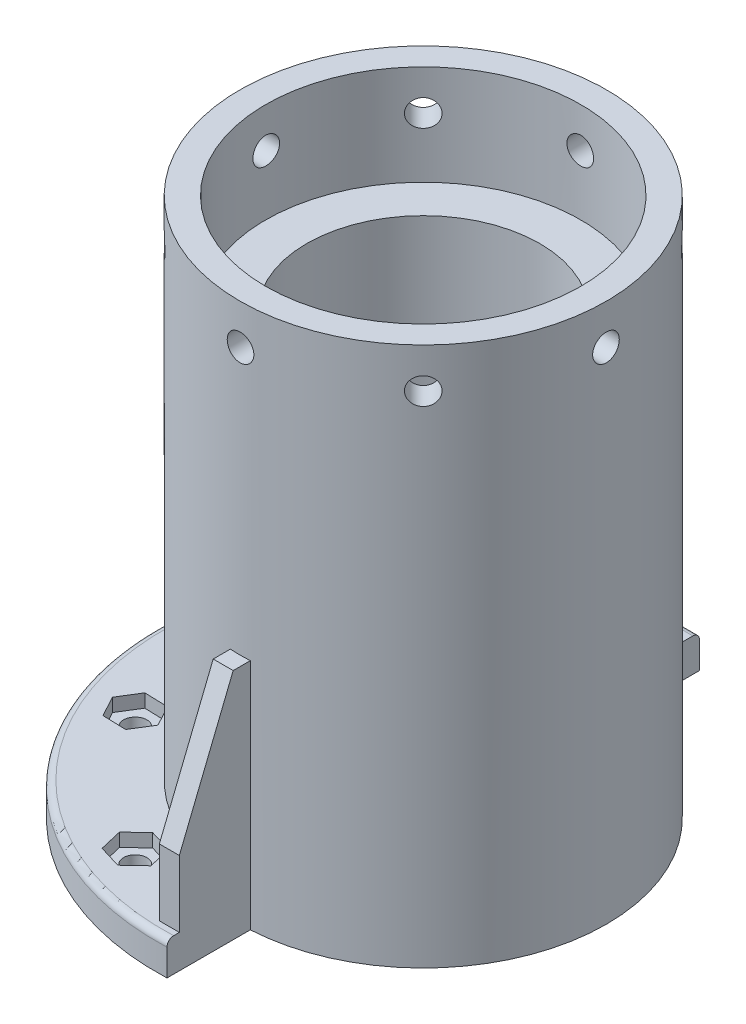
SolidWorks part; units mm, degrees
ref_plane "Front Plane" through (0, 0, 0) normal (0, 0, 1) x (1, 0, 0)
ref_plane "Top Plane" through (0, 0, 0) normal (0, 1, 0) x (1, 0, 0)
ref_plane "Right Plane" through (0, 0, 0) normal (1, 0, 0) x (0, 0, -1)
sketch "Sketch1" plane through (0, 0, 0) normal (0, 1, 0) x (1, 0, 0)
  circle A0 centre (0, 0) radius 23.65
  circle A1 centre (0, 0) radius 27.5
  dimension "D1" = 47.3
  dimension "D2" = 55
extrude "Boss-Extrude1" add sketch "Sketch1" along normal blind 30
sketch "Sketch2" plane through (0, 0, 0) normal (0, 0, 1) x (1, 0, 0)
  line L0 (27.5, 30) -> (-27.5, 30) construction
  circle A0 centre (0, 24) radius 2
  dimension "D2" = 4
  dimension "D1" = 6
extrude "Cut-Extrude1" cut sketch "Sketch2" against normal through all both and the other way through all
pattern_circular "CirPattern1" count 4 every 45 about axis through (0, 30, 0) along (0, 1, 0) of "Cut-Extrude1"
sketch "Sketch3" plane through (0, 0, 0) normal (0, -1, 0) x (1, 0, 0)
  circle A0 centre (0, 0) radius 27.5
  circle A1 centre (0, 0) radius 23.65
extrude "Boss-Extrude2" add sketch "Sketch3" along normal blind 51
sketch "Sketch4" plane through (0, -51, 0) normal (0, -1, 0) x (1, 0, 0)
  line L0 (1.5, 39.9719) -> (1.5, -39.9719)
  arc A0 (1.5, 39.9719) -> (1.5, -39.9719) centre (0, 0) ccw
  circle M1 centre (0, 0) radius 27.5
  dimension "D1" = 80
  dimension "D2" = 1.5
extrude "Boss-Extrude3" add sketch "Sketch4" against normal blind 5 contours L0 A0 M1 | L0 M1
sketch "Sketch6" plane through (0, -46, 0) normal (0, 1, 0) x (1, 0, 0)
  line L0 (1.5, 27.4591) -> (1.5, 39.9719) construction
  line L1 (1.5, 36.6445) -> (-1.5, 36.6445)
  line L2 (1.5, 36.6445) -> (1.5, 24.6445)
  line L3 (1.5, 24.6445) -> (-1.5, 24.6445)
  line L4 (-1.5, 36.6445) -> (-1.5, 24.6445)
  line L5 (1.5, -39.9719) -> (1.5, -27.4591) construction
  line L6 (-36.7098, 1.2195) -> (-24.7098, 1.2195)
  line L7 (-36.7098, 1.2195) -> (-36.7098, -1.7805)
  line L8 (-36.7098, -1.7805) -> (-24.7098, -1.7805)
  line L9 (-24.7098, 1.2195) -> (-24.7098, -1.7805)
  line L10 (1.5, -38.1145) -> (-1.5, -38.1145)
  line L11 (1.5, -38.1145) -> (1.5, -26.1145)
  line L12 (1.5, -26.1145) -> (-1.5, -26.1145)
  line L13 (-1.5, -38.1145) -> (-1.5, -26.1145)
  dimension "D1" = 3
  dimension "D2" = 12
  dimension "D3" = 12
  dimension "D4" = 3
  dimension "D5" = 3
  dimension "D6" = 12
extrude "Boss-Extrude4" add sketch "Sketch6" along normal blind 30
chamfer "Chamfer1" distance 20 angle 22 3 edges at (0, -16, -36.6445) (-36.7098, -16, 0.2805) (0, -16, 38.1145)
sketch "Sketch7" plane through (0, -46, 0) normal (0, 1, 0) x (1, 0, 0)
  line L0 (0, 0) -> (-12.6635, 30.5724) construction
  line L1 (1.5, 36.6445) -> (1.5, 39.9719) construction
  circle A0 centre (-12.6635, 30.5724) radius 1.75
  dimension "D1" = 3.5
  dimension "D2" = 22.5
extrude "Cut-Extrude2" cut sketch "Sketch7" against normal through all
sketch "Sketch8" plane through (0, -46, 0) normal (0, 1, 0) x (1, 0, 0)
  line L1 (-9.5616, 32.2402) -> (-12.5569, 34.0926)
  line L2 (-12.5569, 34.0926) -> (-15.6588, 32.4249)
  line L3 (-15.6588, 32.4249) -> (-15.7654, 28.9046)
  line L4 (-15.7654, 28.9046) -> (-12.7701, 27.0522)
  line L5 (-12.7701, 27.0522) -> (-9.6682, 28.72)
  line L6 (-9.6682, 28.72) -> (-9.5616, 32.2402)
  circle A0 centre (-12.6635, 30.5724) radius 3.05 construction
  dimension "D1" = 6.1
extrude "Cut-Extrude3" cut sketch "Sketch8" against normal blind 2
pattern_circular "CirPattern2" count 4 every 45 about axis through (0, 0, 0) along (0, 1, 0) of "Cut-Extrude2", "Cut-Extrude3"
fillet "Fillet1" radius 1 1 edges at (-40, -46, 0)
sketch "Sketch9" plane through (0, 0, 0) normal (0, 1, 0) x (1, 0, 0)
  circle A0 centre (0, 0) radius 26.2333
  circle A1 centre (0, 0) radius 17.5
  dimension "D1" = 35
extrude "Boss-Extrude5" add sketch "Sketch9" along normal blind 15 and the other way blind 51
